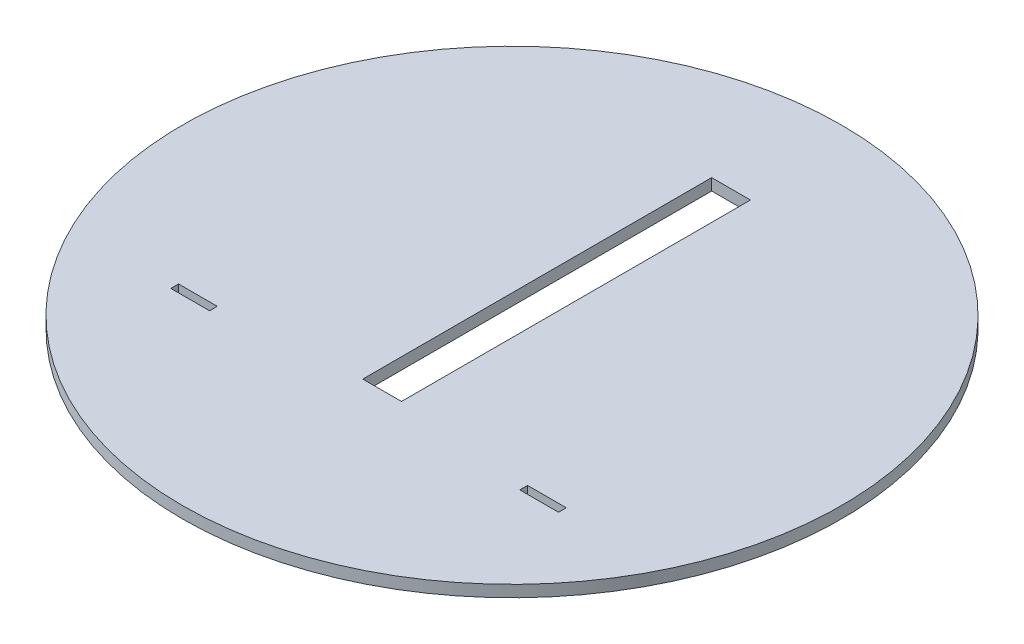
SolidWorks part; units mm, degrees
material "Acrylic (Medium-high impact)"
ref_plane "Front Plane" through (0, 0, 0) normal (0, 0, 1) x (1, 0, 0)
ref_plane "Top Plane" through (0, 0, 0) normal (0, 1, 0) x (1, 0, 0)
ref_plane "Right Plane" through (0, 0, 0) normal (1, 0, 0) x (0, 0, -1)
sketch "Sketch1" plane through (0, 0, 0) normal (0, 1, 0) x (1, 0, 0)
  circle A0 centre (0, 0) radius 8.5
  dimension "D1" = 17
extrude "Boss-Extrude1" add sketch "Sketch1" along normal mid plane 0.3
sketch "Sketch2" plane through (0, 0.15, 0) normal (0, 1, 0) x (1, 0, 0)
  line L0 (0, 0) -> (0, 1.15) construction
  line L1 (0.5, -3.35) -> (-0.5, -3.35)
  line L2 (0.5, -3.35) -> (0.5, 5.65)
  line L3 (0.5, 5.65) -> (-0.5, 5.65)
  line L4 (-0.5, -3.35) -> (-0.5, 5.65)
  line L5 (0.5, -3.35) -> (-0.5, 5.65) construction
  line L6 (0.5, 5.65) -> (-0.5, -3.35) construction
  line L7 (4, -3.7) -> (0.5, -3.7) construction
  line L8 (5, -3.8) -> (4, -3.8)
  line L9 (5, -3.8) -> (5, -3.6)
  line L10 (5, -3.6) -> (4, -3.6)
  line L11 (4, -3.8) -> (4, -3.6)
  line L12 (-4, -3.8) -> (-5, -3.8)
  line L13 (-4, -3.8) -> (-4, -3.6)
  line L14 (-4, -3.6) -> (-5, -3.6)
  line L15 (-5, -3.8) -> (-5, -3.6)
  line L16 (-4, -3.7) -> (-0.5, -3.7) construction
  point P0 (0, 0)
  dimension "D1" = 9
  dimension "D2" = 1
  dimension "D3" = 1.15
  dimension "D4" = 1
  dimension "D5" = 0.2
  dimension "D6" = 10
  dimension "D7" = 0.45
extrude "Cut-Extrude1" cut sketch "Sketch2" against normal up to next
